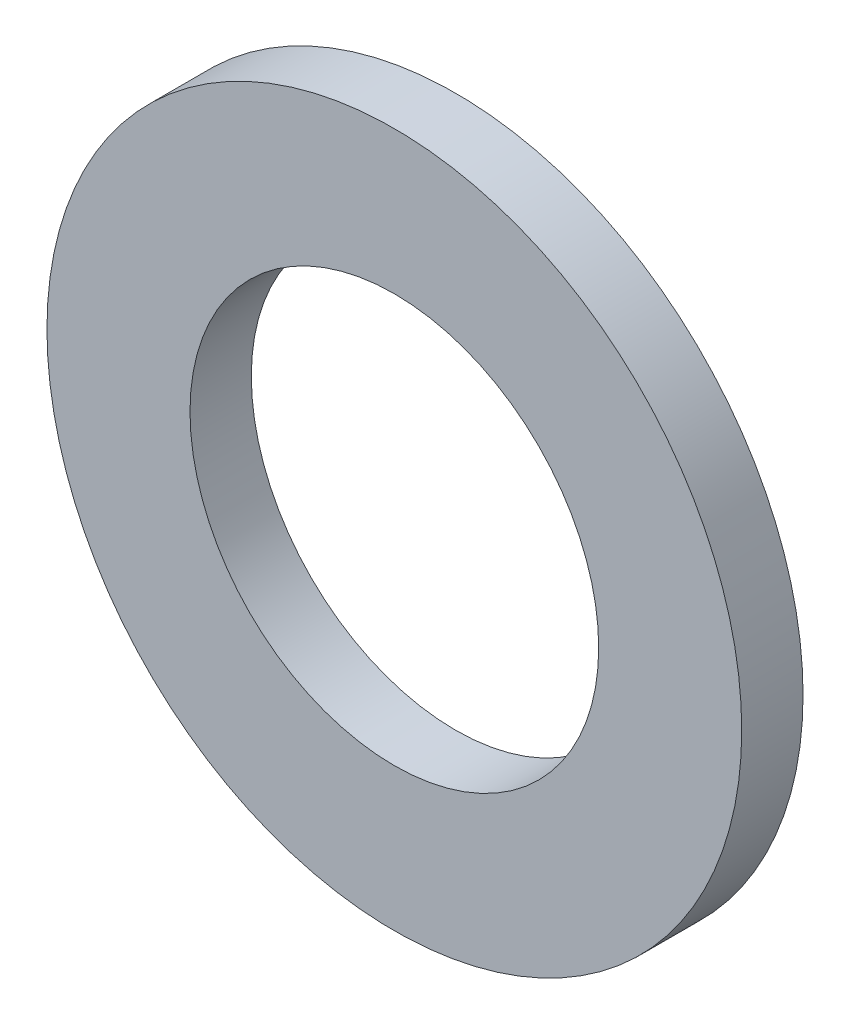
SolidWorks part; units mm, degrees
ref_plane "Front Plane" through (0, 0, 0) normal (0, 0, 1) x (1, 0, 0)
ref_plane "Top Plane" through (0, 0, 0) normal (0, 1, 0) x (1, 0, 0)
ref_plane "Right Plane" through (0, 0, 0) normal (1, 0, 0) x (0, 0, -1)
sketch "Sketch1" plane through (0, 0, 0) normal (0, 0, 1) x (1, 0, 0)
  circle A0 centre (0, 0) radius 5
  circle A1 centre (0, 0) radius 8.5
  dimension "D1" = 10
  dimension "D2" = 17
extrude "Boss-Extrude1" add sketch "Sketch1" along normal blind 1.5
